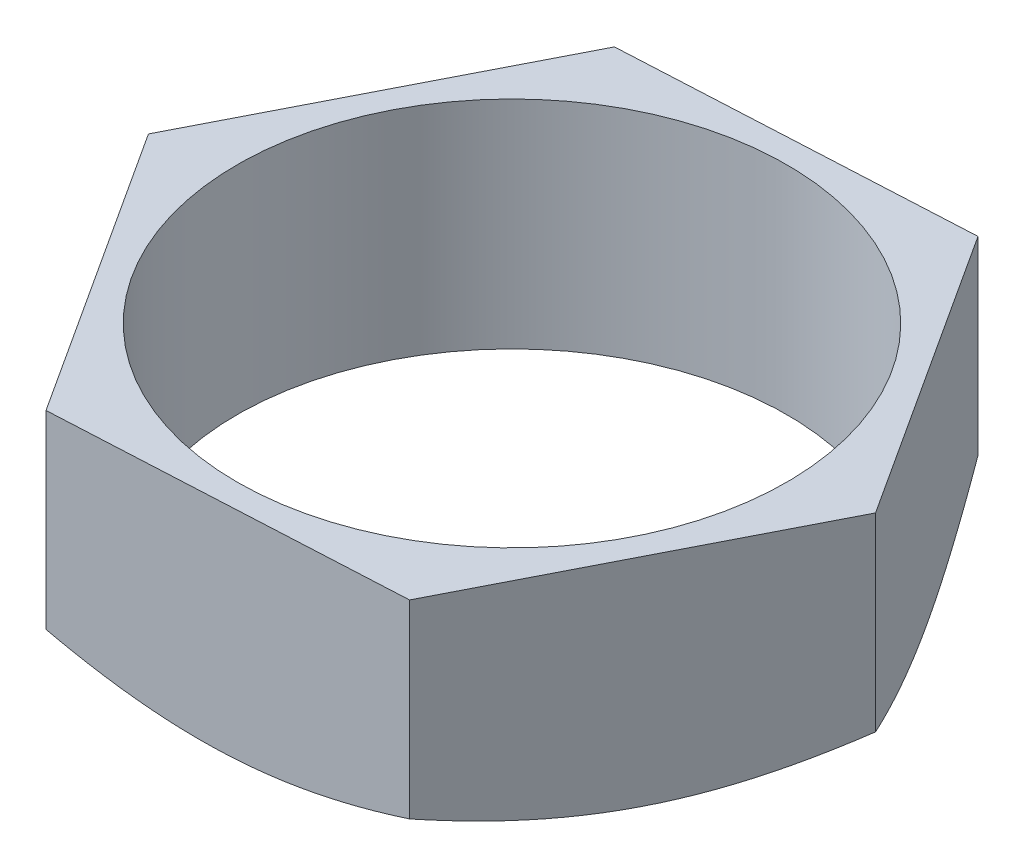
SolidWorks part; units mm, degrees
ref_plane "Front Plane" through (0, 0, 0) normal (0, 0, 1) x (1, 0, 0)
ref_plane "Top Plane" through (0, 0, 0) normal (0, 1, 0) x (1, 0, 0)
ref_plane "Right Plane" through (0, 0, 0) normal (1, 0, 0) x (0, 0, -1)
sketch "Sketch4" plane through (0, 0, 0) normal (0, 1, 0) x (1, 0, 0)
  line L1 (3.641, 7.1234) -> (-4.3486, 6.7149)
  line L2 (-4.3486, 6.7149) -> (-7.9896, -0.4086)
  line L3 (-7.9896, -0.4086) -> (-3.641, -7.1234)
  line L4 (-3.641, -7.1234) -> (4.3486, -6.7149)
  line L5 (4.3486, -6.7149) -> (7.9896, 0.4086)
  line L6 (7.9896, 0.4086) -> (3.641, 7.1234)
  circle A0 centre (0, 0) radius 8 construction
  circle A1 centre (0, 0) radius 6.9282 construction
  circle A2 centre (0, 0) radius 6.35
  dimension "D1" = 16
  dimension "D2" = 12.7
extrude "Boss-Extrude1" add sketch "Sketch4" along normal blind 5
sketch "Sketch9" plane through (0, 0, 0) normal (0, -1, 0) x (1, 0, 0)
  circle A0 centre (0, 0) radius 6.9282
extrude "Cut-Extrude1" cut sketch "Sketch9" against normal through all draft 60 flip side to cut
